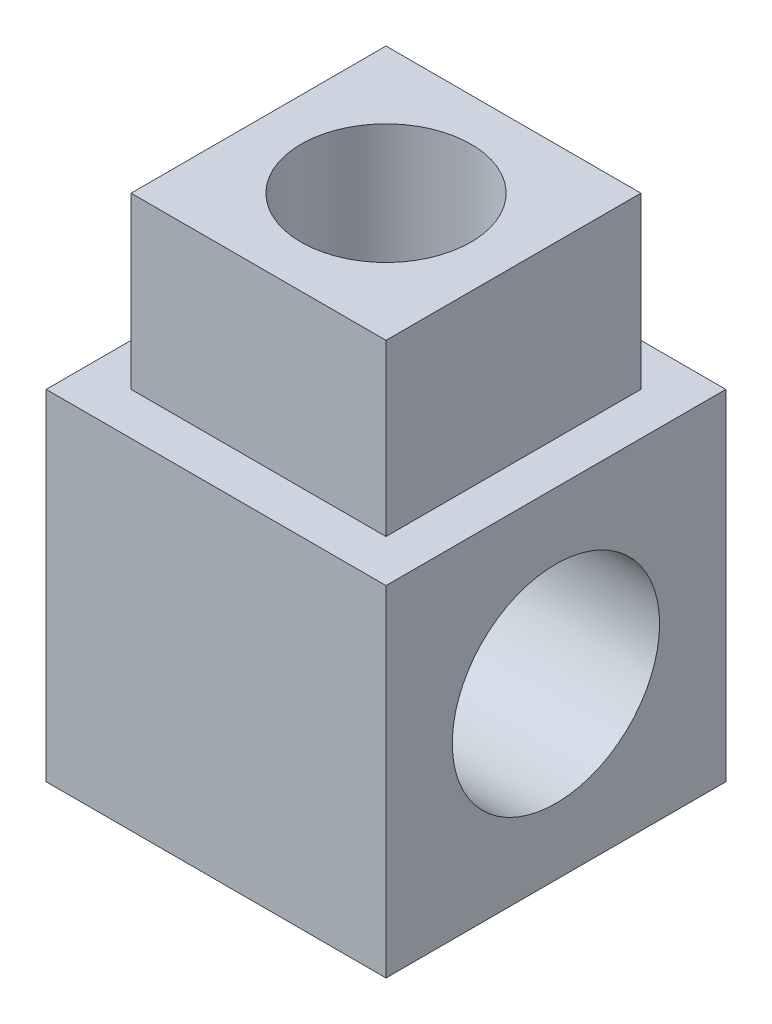
SolidWorks part; units mm, degrees
ref_plane "Front Plane" through (0, 0, 0) normal (0, 0, 1) x (1, 0, 0)
ref_plane "Top Plane" through (0, 0, 0) normal (0, 1, 0) x (1, 0, 0)
ref_plane "Right Plane" through (0, 0, 0) normal (1, 0, 0) x (0, 0, -1)
sketch "Sketch1" plane through (0, 0, 0) normal (1, 0, 0) x (0, 0, -1)
  line L1 (-10, 10) -> (10, 10)
  line L2 (-10, 10) -> (-10, -10)
  line L3 (-10, -10) -> (10, -10)
  line L4 (10, 10) -> (10, -10)
  line L5 (-10, 10) -> (10, -10) construction
  line L6 (-10, -10) -> (10, 10) construction
  circle A0 centre (0, 0) radius 6.1
  dimension "D1" = 12.2
  dimension "D2" = 20
  dimension "D3" = 20
extrude "Boss-Extrude1" add sketch "Sketch1" along normal mid plane 20
sketch "Sketch2" plane through (0, 10, 0) normal (0, 1, 0) x (1, 0, 0)
  line L1 (-7.5, 7.5) -> (7.5, 7.5)
  line L2 (-7.5, 7.5) -> (-7.5, -7.5)
  line L3 (-7.5, -7.5) -> (7.5, -7.5)
  line L4 (7.5, 7.5) -> (7.5, -7.5)
  line L5 (-7.5, 7.5) -> (7.5, -7.5) construction
  line L6 (-7.5, -7.5) -> (7.5, 7.5) construction
  point P0 (0, 0)
  dimension "D1" = 15
  dimension "D2" = 15
extrude "Boss-Extrude2" add sketch "Sketch2" along normal blind 10
sketch "Sketch3" plane through (0, 20, 0) normal (0, 1, 0) x (1, 0, 0)
  circle A0 centre (0, 0) radius 5
extrude "Cut-Extrude1" cut sketch "Sketch3" against normal blind 10
